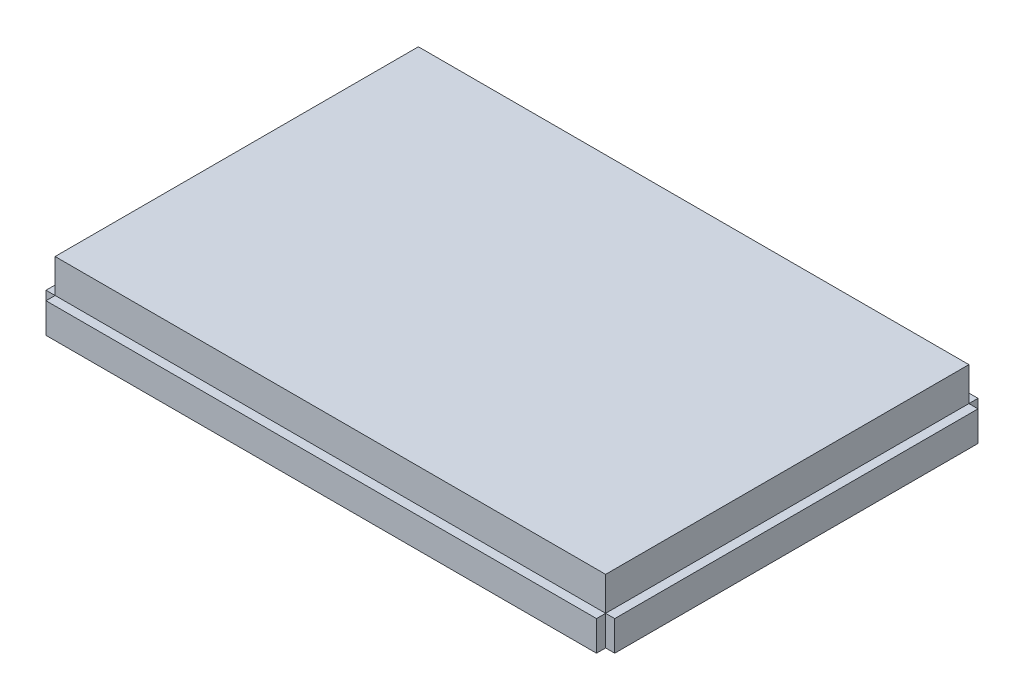
SolidWorks part; units mm, degrees
ref_plane "Front Plane" through (0, 0, 0) normal (0, 0, 1) x (1, 0, 0)
ref_plane "Top Plane" through (0, 0, 0) normal (0, 1, 0) x (1, 0, 0)
ref_plane "Right Plane" through (0, 0, 0) normal (1, 0, 0) x (0, 0, -1)
sketch "Sketch1" plane through (0, 0, 0) normal (0, 1, 0) x (1, 0, 0)
  line L1 (41.1099, -27.1272) -> (-41.1099, -27.1272)
  line L2 (41.1099, -27.1272) -> (41.1099, 27.1272)
  line L3 (41.1099, 27.1272) -> (-41.1099, 27.1272)
  line L4 (-41.1099, -27.1272) -> (-41.1099, 27.1272)
  line L5 (41.1099, -27.1272) -> (-41.1099, 27.1272) construction
  line L6 (41.1099, 27.1272) -> (-41.1099, -27.1272) construction
  point P0 (0, 0)
  dimension "D1" = 54.2544
  dimension "D2" = 82.2198
extrude "Boss-Extrude1" add sketch "Sketch1" along normal blind 9.525
sketch "Sketch2" plane through (0, 0, 27.1272) normal (0, 0, 1) x (1, 0, 0)
  line L0 (-41.1099, 9.525) -> (-41.1099, 0) construction
  line L1 (-41.1099, 4.4831) -> (41.1099, 4.4831)
  line L2 (-41.1099, 4.4831) -> (-41.1099, 0)
  line L3 (-41.1099, 0) -> (41.1099, 0)
  line L4 (41.1099, 4.4831) -> (41.1099, 0)
  line L5 (41.1099, 9.525) -> (41.1099, 0) construction
  line L6 (-41.1099, 0) -> (41.1099, 0) construction
  dimension "D1" = 4.4831
extrude "Boss-Extrude2" add sketch "Sketch2" along normal blind 1.3589
mirror "Mirror1" about plane through (0, 0, 0) normal (0, 0, 1) of "Boss-Extrude2"
sketch "Sketch3" plane through (41.1099, 0, 0) normal (1, 0, 0) x (0, 0, -1)
  line L0 (-28.4861, 0) -> (28.4861, 0) construction
  line L1 (-27.1272, 4.4831) -> (27.1272, 4.4831)
  line L2 (-27.1272, 4.4831) -> (-27.1272, 0)
  line L3 (-27.1272, 0) -> (27.1272, 0)
  line L4 (27.1272, 4.4831) -> (27.1272, 0)
  line L5 (27.1272, 9.525) -> (27.1272, 4.4831) construction
extrude "Boss-Extrude3" add sketch "Sketch3" along normal blind 1.3589
mirror "Mirror2" about plane through (0, 0, 0) normal (1, 0, 0) of "Boss-Extrude3"
